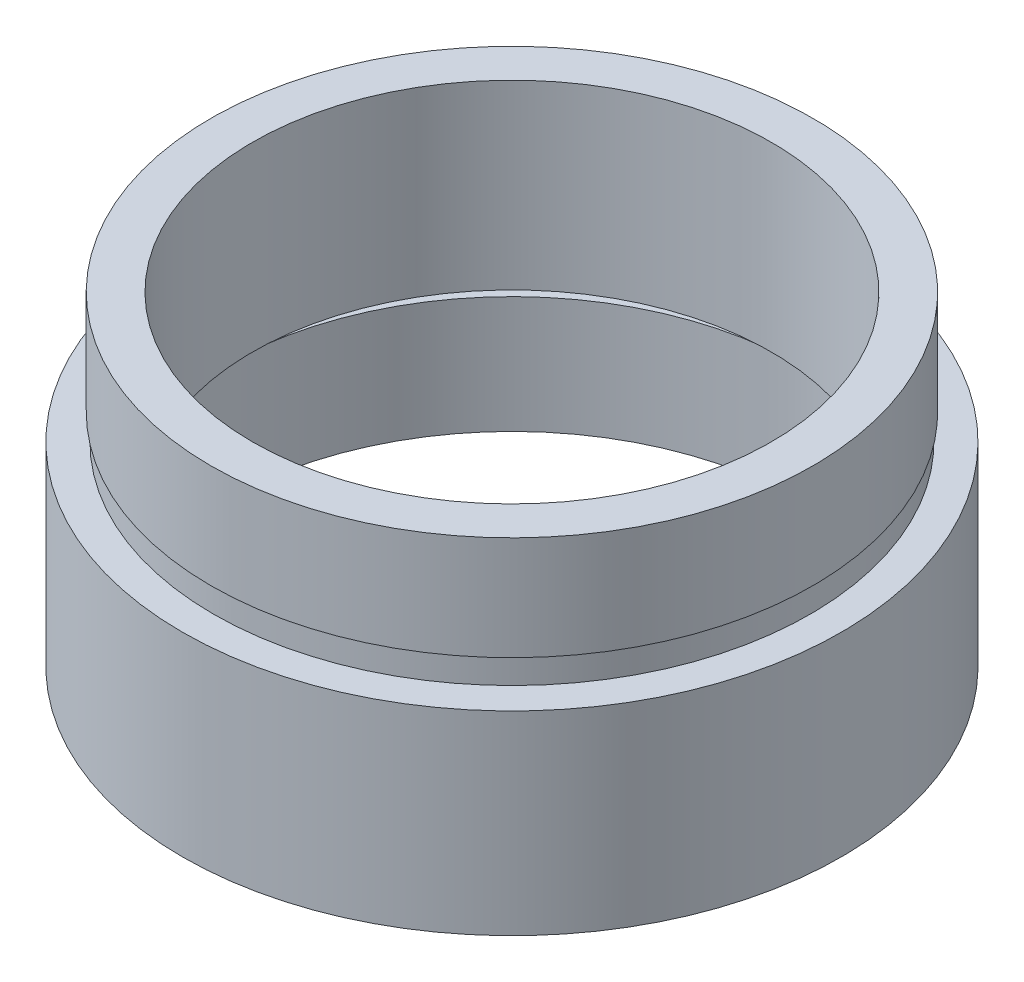
SolidWorks part; units mm, degrees
ref_plane "前视基准面" through (0, 0, 0) normal (0, 0, 1) x (1, 0, 0)
ref_plane "上视基准面" through (0, 0, 0) normal (0, 1, 0) x (1, 0, 0)
ref_plane "右视基准面" through (0, 0, 0) normal (1, 0, 0) x (0, 0, -1)
sketch "草图1" plane through (0, 0, 0) normal (0, 0, 1) x (1, 0, 0)
  line L0 (0, 161.3762) -> (0, 0) construction
  line L1 (141.7365, 0) -> (-131.7984, 0) construction
  line L2 (12.7, 0) -> (12.7, 7.5)
  line L3 (11.1, 4.5) -> (11.7, 4.5)
  line L4 (11.1, 0) -> (12.7, 0)
  line L5 (11.7, 4.5) -> (11.7, 5.5)
  line L6 (10, 5.5) -> (10, 12.5)
  line L7 (11.1, 4.5) -> (11.1, 0)
  line L8 (11.7, 5.5) -> (10, 5.5)
  line L9 (11.5, 8.5) -> (11.5, 7.5)
  line L10 (12.7, 7.5) -> (11.5, 7.5)
  line L11 (11.6, 8.5) -> (11.6, 12.5)
  line L12 (11.5, 8.5) -> (11.6, 8.5)
  line L13 (11.6, 12.5) -> (10, 12.5)
  dimension "D2" = 12.7
  dimension "D3" = 11.7
  dimension "D4" = 10
  dimension "D5" = 11.5
  dimension "D6" = 11.6
  dimension "D7" = 1
  dimension "D8" = 7.5
  dimension "D9" = 5
  dimension "D10" = 1
  dimension "D11" = 11.1
  dimension "D12" = 4.5
revolve "旋转1" add sketch "草图1" angle 360 about L0
cosmetic thread "装饰螺纹线1" parameters "D2"=23.2
cosmetic thread "装饰螺纹线2" parameters "D2"=21
cosmetic thread "装饰螺纹线3" parameters "D2"=23
